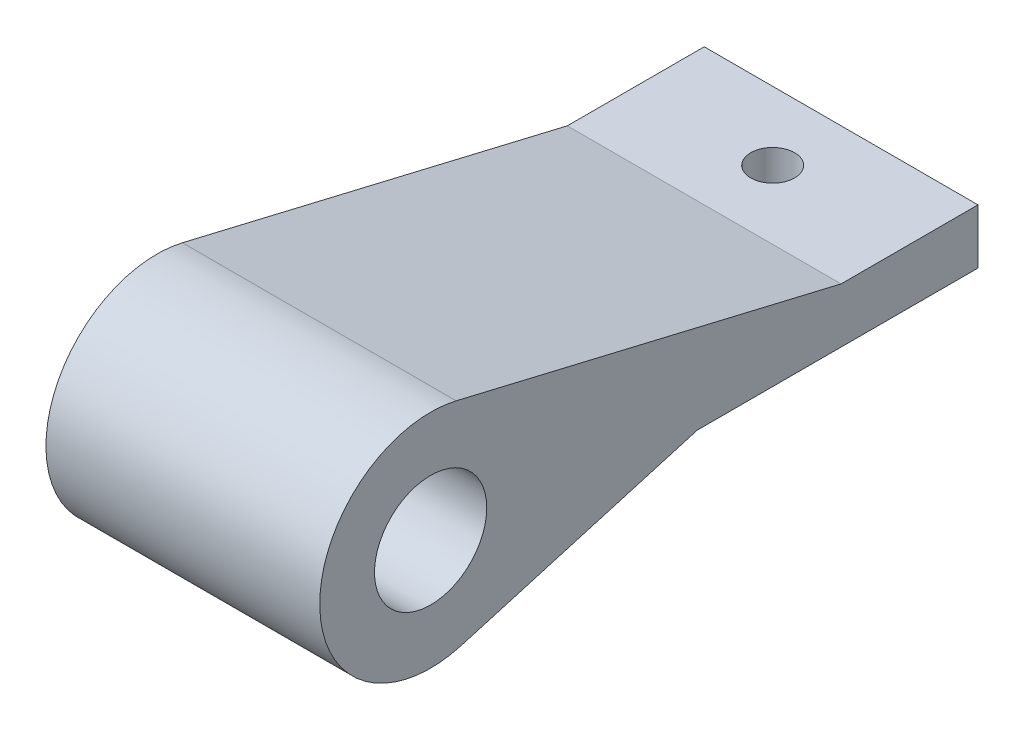
SolidWorks part; units mm, degrees
ref_plane "Front Plane" through (0, 0, 0) normal (0, 0, 1) x (1, 0, 0)
ref_plane "Top Plane" through (0, 0, 0) normal (0, 1, 0) x (1, 0, 0)
ref_plane "Right Plane" through (0, 0, 0) normal (1, 0, 0) x (0, 0, -1)
sketch "Sketch1" plane through (0, 0, 0) normal (1, 0, 0) x (0, 0, -1)
  line L0 (-10.25, 0) -> (10.25, 0)
  line L2 (0.25, 4) -> (10.25, 4)
  line L3 (10.25, 4) -> (10.25, 0)
  line L4 (-10.25, 0) -> (-27.4788, -5)
  line L5 (0.25, 4) -> (-27.8693, 10.6609)
  circle A0 centre (-29.7363, 2.779) radius 4.1
  arc A1 (-27.8693, 10.6609) -> (-27.4788, -5) centre (-29.7363, 2.779) ccw
  circle A2 centre (-29.7363, 2.779) radius 8.1 construction
  point P5 (0, 0)
  point P7 (-9.293, 14.7926)
  point P9 (-9.7709, 12.6819)
  point P14 (-9.6911, 8.7272)
  point P15 (-8.1315, 12.6329)
  point P16 (-22.4974, 8.5142)
  point P17 (-27.5725, 8.05)
  point P18 (-7.5, 4)
  point P19 (-27.4788, -1.3701)
  point P20 (-11.25, 4)
  point P21 (-8.6385, 4)
  dimension "D1" = 8.2
  dimension "D2" = 20.5
  dimension "D3" = 4
  dimension "D5" = 5
  dimension "D6" = 10
  dimension "D4" = 4
extrude "Boss-Extrude1" add sketch "Sketch1" along normal blind 20
sketch "Sketch2" plane through (0, 4, 0) normal (0, 1, 0) x (1, 0, 0)
  line L0 (20, 10.25) -> (20, 0.25) construction
  line L1 (20, 10.25) -> (0, 10.25) construction
  circle A0 centre (10, 5.25) radius 1.6
  point P4 (20, 5.25)
  point P7 (10, 10.25)
  dimension "D1" = 3.2
extrude "Cut-Extrude1" cut sketch "Sketch2" against normal through all
